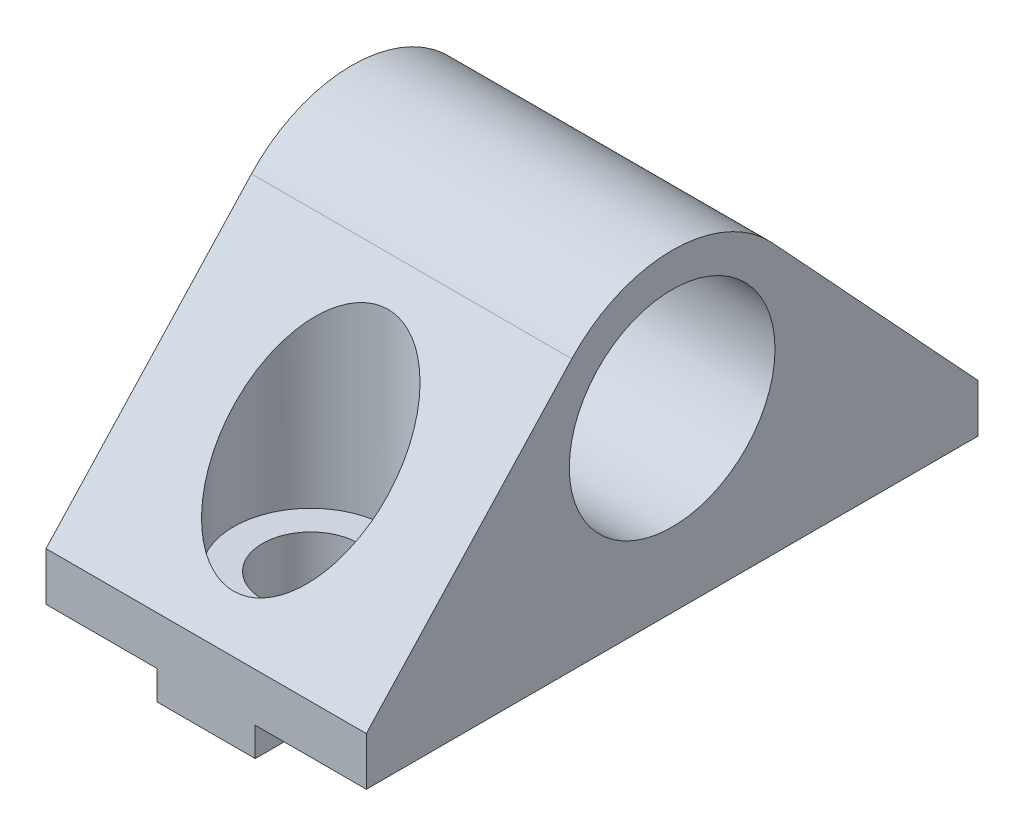
SolidWorks part; units mm, degrees
material "ABS"
ref_plane "Front Plane" through (0, 0, 0) normal (0, 0, 1) x (1, 0, 0)
ref_plane "Top Plane" through (0, 0, 0) normal (0, 1, 0) x (1, 0, 0)
ref_plane "Right Plane" through (0, 0, 0) normal (1, 0, 0) x (0, 0, -1)
sketch "Sketch1" plane through (0, 0, 0) normal (0, 0, 1) x (1, 0, 0)
  line L0 (101.6062, 195.4843) -> (108.5162, 195.4843)
  line L1 (108.5162, 195.4843) -> (108.5162, 193.6843)
  line L2 (108.5162, 193.6843) -> (114.6049, 193.6843)
  line L3 (114.6049, 193.6843) -> (114.6049, 195.4843)
  line L4 (114.6049, 195.4843) -> (121.5062, 195.4843)
  line L5 (121.5062, 195.4843) -> (121.5062, 198.4843)
  line L6 (121.5062, 198.4843) -> (101.6062, 198.4843)
  line L7 (101.6062, 198.4843) -> (101.6062, 195.4843)
  dimension "D1" = 3
  dimension "D2" = 1.8
  dimension "D3" = 19.9
  dimension "D4" = 6.91
extrude "Boss-Extrude1" add sketch "Sketch1" against normal blind 38
sketch "Sketch2" plane through (101.6062, 0, 0) normal (-1, 0, 0) x (0, 0, 1)
  line L0 (-38, 198.4843) -> (-25.2351, 212.2613)
  line L1 (-38, 198.4843) -> (0, 198.4843) construction
  line L2 (-12.7649, 212.2613) -> (0, 198.4843)
  line L3 (0, 198.4843) -> (-38, 198.4843)
  line L4 (-19, 198.4843) -> (-19, 206.4843) construction
  arc A0 (-25.2351, 212.2613) -> (-12.7649, 212.2613) centre (-19, 206.4843) cw
  circle A1 centre (-19, 206.4843) radius 6.39
  dimension "D2" = 8.5
  dimension "D3" = 12.78
  dimension "D1" = 8
extrude "Boss-Extrude2" add sketch "Sketch2" against normal up to vertex (19.9 mm away) up to point (121.5062, 198.4843, -38)
ref_plane "Plane1" through (111.5562, 0, 0) normal (-1, 0, 0) x (0, 0, 1)
sketch "Sketch3" plane through (111.5562, 0, 0) normal (-1, 0, 0) x (0, 0, 1)
  line L0 (-26.7, 211.67) -> (-26.7, 198.9857)
  line L1 (-26.7, 198.9857) -> (-28.5, 198.9857)
  line L2 (-28.5, 198.9857) -> (-28.5, 189.9061)
  line L3 (-28.5, 189.9061) -> (-31.5, 189.9061)
  line L4 (-31.5, 189.9061) -> (-31.5, 211.67)
  line L5 (-31.5, 211.67) -> (-26.7, 211.67)
  dimension "D1" = 4.8
  dimension "D2" = 3
  dimension "D3" = 3.5014
  dimension "D4" = 6.5
revolve "Cut-Revolve1" cut sketch "Sketch3" angle 360 about L4
ref_plane "Plane2" through (0, 0, -19) normal (0, 0, -1) x (-1, 0, 0)
mirror "Mirror1" about plane through (0, 0, -19) normal (0, 0, -1) of "Cut-Revolve1"
